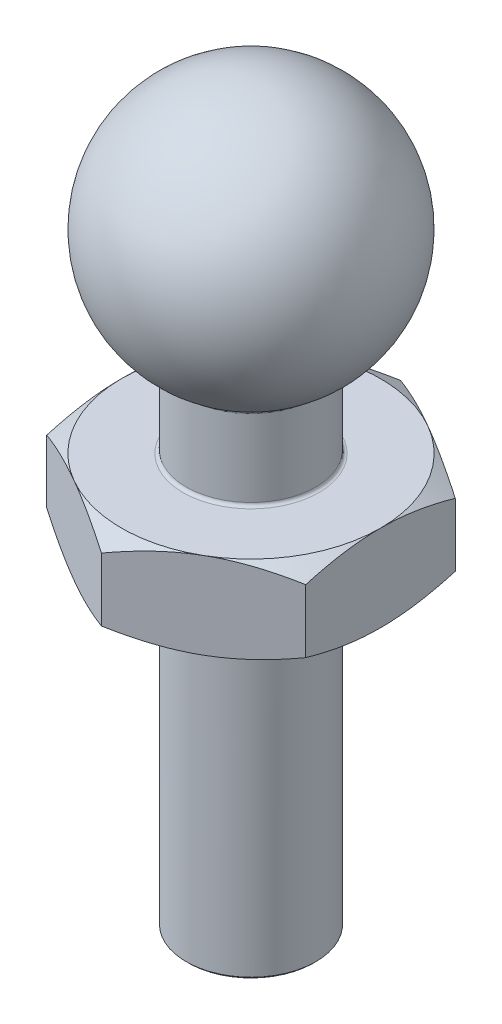
SolidWorks part; units mm, degrees
ref_plane "Front Plane" through (0, 0, 0) normal (0, 0, 1) x (1, 0, 0)
ref_plane "Top Plane" through (0, 0, 0) normal (0, 1, 0) x (1, 0, 0)
ref_plane "Right Plane" through (0, 0, 0) normal (1, 0, 0) x (0, 0, -1)
sketch "Sketch1" plane through (0, 0, 0) normal (0, 0, 1) x (1, 0, 0)
  line L1 (0, 0) -> (1.5, 0)
  line L2 (1.5, 0) -> (1.5, 11.4019)
  line L3 (0, 0) -> (0, 11)
  line L4 (0, 11) -> (0, 17)
  circle A0 centre (0, 14) radius 3 construction
  arc A1 (0, 17) -> (1.5, 11.4019) centre (0, 14) cw
  dimension "D1" = 6
  dimension "D2" = 1.5
  dimension "D3" = 11
revolve "Revolve1" add sketch "Sketch1" angle 360 about L4
sketch "Sketch2" plane through (0, 0, 0) normal (0, 0, 1) x (1, 0, 0)
  line L0 (-6.9712, 7.5) -> (6.9712, 7.5)
  line L1 (-1.5, 0) -> (1.5, 0) construction
  point P4 (0, 7.5)
  dimension "D1" = 7.5
split line "Split Line1"
chamfer "Chamfer1" distance 0.05 angle 45 1 edges at (0, 0, -1.5)
ref_plane "Plane1" through (0, 7.5, 0) normal (0, 1, 0) x (1, 0, 0)
sketch "Sketch3" plane through (0, 7.5, 0) normal (0, 1, 0) x (1, 0, 0)
  line L1 (-3, -1.7321) -> (0, -3.4641)
  line L2 (0, -3.4641) -> (3, -1.7321)
  line L3 (3, -1.7321) -> (3, 1.7321)
  line L4 (3, 1.7321) -> (0, 3.4641)
  line L5 (0, 3.4641) -> (-3, 1.7321)
  line L6 (-3, 1.7321) -> (-3, -1.7321)
  circle A0 centre (0, 0) radius 1.5
  circle A1 centre (0, 0) radius 3 construction
  circle A2 centre (0, 0) radius 1.5 construction
  dimension "D1" = 6
extrude "Boss-Extrude1" add sketch "Sketch3" along normal blind 2
sketch "Sketch4" plane through (0, 7.5, 0) normal (0, -1, 0) x (1, 0, 0)
  circle A0 centre (0, 0) radius 3 construction
  circle A1 centre (0, 0) radius 3
extrude "Cut-Extrude1" cut sketch "Sketch4" against normal blind 2 draft 60 flip side to cut
sketch "Sketch6" plane through (0, 9.5, 0) normal (0, 1, 0) x (1, 0, 0)
  circle A1 centre (0, 0) radius 3
  circle A2 centre (0, 0) radius 3
  dimension "D1" = 0
extrude "Cut-Extrude2" cut sketch "Sketch6" against normal blind 2 draft 60 flip side to cut
fillet "Fillet1" radius 0.075 2 edges at (0, 11.4019, -1.5) (0, 9.5, 1.5)
